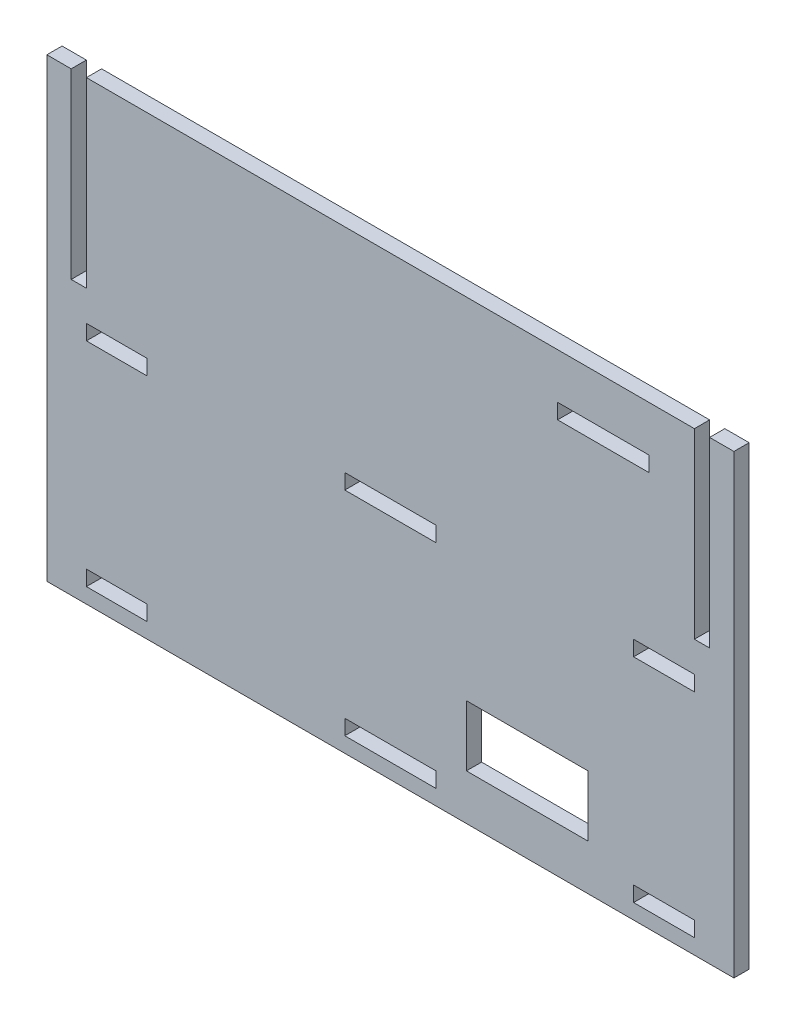
SolidWorks part; units mm, degrees
ref_plane "Plan de face" through (0, 0, 0) normal (0, 0, 1) x (1, 0, 0)
ref_plane "Plan de dessus" through (0, 0, 0) normal (0, 1, 0) x (1, 0, 0)
ref_plane "Plan de droite" through (0, 0, 0) normal (1, 0, 0) x (0, 0, -1)
sketch "Esquisse1" plane through (0, 0, 0) normal (0, 0, 1) x (1, 0, 0)
  line L0 (0, 150) -> (0, 0) construction
  line L1 (80, 10) -> (100, 10)
  line L2 (80, 80) -> (100, 80)
  line L3 (80, 80) -> (80, 75)
  line L4 (80, 75) -> (100, 75)
  line L5 (-100, 150) -> (100, 150)
  line L6 (100, 150) -> (100, 90)
  line L7 (100, 90) -> (105, 90)
  line L8 (105, 90) -> (105, 150)
  line L9 (105, 150) -> (113, 150)
  line L10 (113, 150) -> (113, 0)
  line L11 (113, 0) -> (-113, 0)
  line L12 (100, 80) -> (100, 75)
  line L13 (80, 10) -> (80, 5)
  line L14 (80, 5) -> (100, 5)
  line L15 (100, 10) -> (100, 5)
  line L16 (-15, 5) -> (15, 5)
  line L17 (15, 5) -> (15, 10)
  line L18 (15, 10) -> (0, 10)
  line L19 (-15, 80) -> (0, 80)
  line L20 (0, 80) -> (0, -70) construction
  line L21 (-15, 75) -> (15, 75)
  line L22 (15, 75) -> (15, 80)
  line L23 (15, 80) -> (0, 80)
  line L24 (-15, 75) -> (-15, 80)
  line L25 (113, 80) -> (113, -70) [skipped]
  line L26 (-15, 10) -> (0, 10)
  line L27 (-15, 5) -> (-15, 10)
  line L28 (-100, 10) -> (-100, 5)
  line L29 (-80, 5) -> (-100, 5)
  line L30 (-80, 10) -> (-80, 5)
  line L31 (-100, 80) -> (-100, 75)
  line L32 (-113, 150) -> (-113, 0)
  line L33 (-105, 150) -> (-113, 150)
  line L34 (-105, 90) -> (-105, 150)
  line L35 (-100, 90) -> (-105, 90)
  line L36 (-100, 150) -> (-100, 90)
  line L37 (-80, 75) -> (-100, 75)
  line L38 (-80, 80) -> (-80, 75)
  line L39 (-80, 80) -> (-100, 80)
  line L40 (-80, 10) -> (-100, 10)
  line L42 (25, 35) -> (65, 35)
  line L43 (25, 35) -> (25, 15)
  line L44 (25, 15) -> (65, 15)
  line L45 (65, 35) -> (65, 15)
  line L46 (55, 135) -> (85, 135)
  line L47 (55, 135) -> (55, 130)
  line L48 (55, 130) -> (85, 130)
  line L49 (85, 135) -> (85, 130)
  point P33 (0, 75)
  point P36 (0, 5)
  point P51 (65, 25)
  dimension "D2" = 150
  dimension "D3" = 60
  dimension "D4" = 20
  dimension "D5" = 8
  dimension "D6" = 5
  dimension "D7" = 5
  dimension "D8" = 40
  dimension "D9" = 75
  dimension "D10" = 15
  dimension "D11" = 5
  dimension "D12" = 100
  dimension "D14" = 20
  dimension "D15" = 5
  dimension "D16" = 15
  dimension "D17" = 5
  dimension "D18" = 30
  dimension "D19" = 15
  dimension "D20" = 15
  dimension "D21" = 70
  dimension "D13" = 2
extrude "Boss.-Extru.1" add sketch "Esquisse1" along normal blind 5
